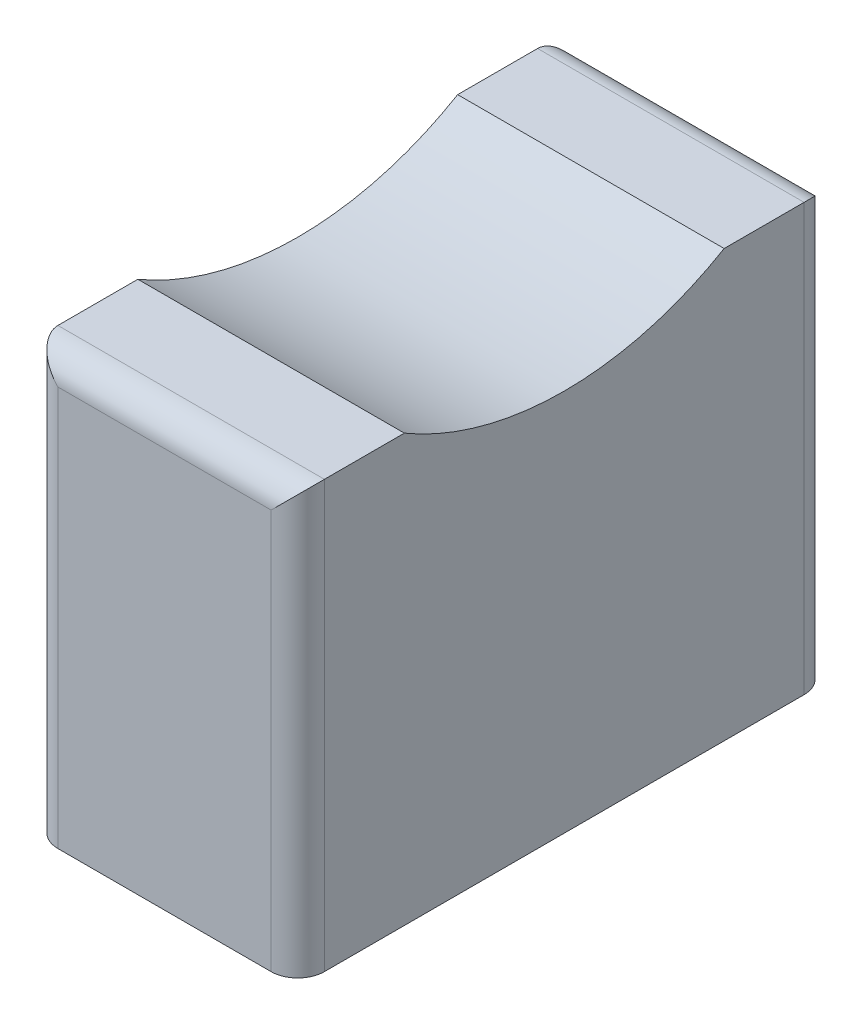
SolidWorks part; units mm, degrees
ref_plane "Front Plane" through (0, 0, 0) normal (0, 0, 1) x (1, 0, 0)
ref_plane "Top Plane" through (0, 0, 0) normal (0, 1, 0) x (1, 0, 0)
ref_plane "Right Plane" through (0, 0, 0) normal (1, 0, 0) x (0, 0, -1)
sketch "Sketch1" plane through (0, 0, 0) normal (0, 1, 0) x (1, 0, 0)
  line L1 (-5, -10) -> (5, -10)
  line L2 (-5, -10) -> (-5, 10)
  line L3 (-5, 10) -> (5, 10)
  line L4 (5, -10) -> (5, 10)
  line L5 (-5, -10) -> (5, 10) construction
  line L6 (-5, 10) -> (5, -10) construction
  point P0 (0, 0)
  dimension "D1" = 20
  dimension "D2" = 10
extrude "Boss-Extrude1" add sketch "Sketch1" along normal blind 16
sketch "Sketch2" plane through (0, 0, 0) normal (0, -1, 0) x (1, 0, 0)
  line L0 (5, 0) -> (-5, 0) construction
  line L1 (5, 10) -> (5, -10) construction
  line L2 (-5, -10) -> (-5, 10) construction
  line L4 (-0.7, 2.15) -> (0.7, 2.15)
  line L5 (-0.7, 2.15) -> (-0.7, -2.15)
  line L6 (-0.7, -2.15) -> (0.7, -2.15)
  line L7 (0.7, 2.15) -> (0.7, -2.15)
  line L8 (-0.7, 2.15) -> (0.7, -2.15) construction
  line L9 (-0.7, -2.15) -> (0.7, 2.15) construction
  point P6 (0, 0)
  dimension "D1" = 4.3
  dimension "D2" = 1.4
extrude "Cut-Extrude1" cut sketch "Sketch2" against normal blind 5
sketch "Sketch6" plane through (5, 0, 0) normal (1, 0, 0) x (0, 0, -1)
  line L0 (-10, 16) -> (10, 16) construction
  line L1 (-10, 16) -> (-10, 0) construction
  line L2 (10, 16) -> (10, 0) construction
  line L3 (-6, 16) -> (6, 16)
  arc A0 (-6, 16) -> (6, 16) centre (0, 26.1988) ccw
  dimension "D1" = 4
  dimension "D2" = 4
extrude "Cut-Extrude2" cut sketch "Sketch6" against normal blind 10
fillet "Fillet2" radius 1 6 edges at (0, 16, -10) (-5, 8, -10) (5, 8, -10) (-5, 8, 10) (5, 8, 10) (0, 16, 10)
